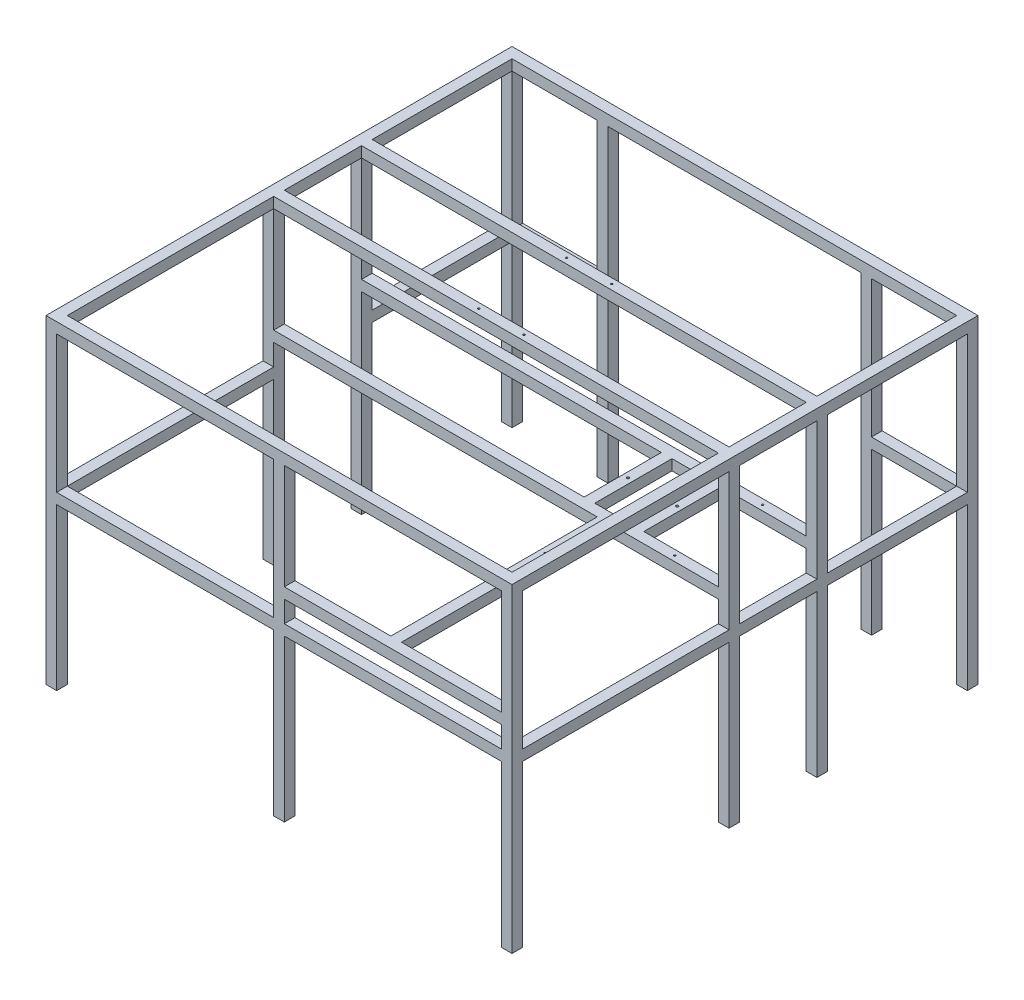
SolidWorks part; units mm, degrees
ref_plane "Front Plane" through (0, 0, 0) normal (0, 0, 1) x (1, 0, 0)
ref_plane "Top Plane" through (0, 0, 0) normal (0, 1, 0) x (1, 0, 0)
ref_plane "Right Plane" through (0, 0, 0) normal (1, 0, 0) x (0, 0, -1)
sketch "Sketch1" plane through (0, 0, 0) normal (0, 1, 0) x (1, 0, 0)
  line L0 (-835, 835) -> (-835, 310)
  line L1 (-875, 875) -> (875, 875)
  line L2 (-875, 875) -> (-875, -875)
  line L3 (-875, -875) -> (875, -875)
  line L4 (875, 875) -> (875, -875)
  line L5 (-875, 875) -> (875, -875) construction
  line L6 (-875, -875) -> (875, 875) construction
  line L7 (-835, -835) -> (835, -835)
  line L8 (835, 835) -> (835, 310)
  line L9 (-835, 835) -> (835, 835)
  line L10 (-835, -20) -> (835, -20)
  line L12 (-835, -60) -> (-835, -835)
  line L13 (-835, 835) -> (-835, -835) construction
  line L14 (835, -60) -> (835, -835)
  line L15 (835, 835) -> (835, -835) construction
  line L16 (835, 20) -> (835, -20)
  line L17 (-835, 20) -> (-835, -20)
  line L18 (-835, -60) -> (835, -60)
  line L19 (835, 270) -> (-835, 270)
  line L20 (835, 310) -> (-835, 310)
  line L21 (835, 270) -> (835, 20)
  line L22 (-835, 270) -> (-835, 20)
  point P0 (0, 0)
  dimension "D1" = 1750
  dimension "D2" = 1750
  dimension "D4" = 40
  dimension "D5" = 20
  dimension "D6" = 40
  dimension "D7" = 40
  dimension "D8" = 290
  dimension "D9" = 40
  dimension "D3" = 40
extrude "Boss-Extrude1" add sketch "Sketch1" along normal blind 40
sketch "Sketch2" plane through (0, 0, 0) normal (0, -1, 0) x (1, 0, 0)
  line L0 (0, 0) -> (0, 835) construction
  line L1 (-835, 835) -> (-875, 835)
  line L2 (-835, 835) -> (-835, 875)
  line L3 (-835, 875) -> (-875, 875)
  line L4 (-875, 835) -> (-875, 875)
  line L5 (835, 835) -> (875, 835)
  line L6 (835, 835) -> (835, 875)
  line L7 (835, 875) -> (875, 875)
  line L8 (875, 835) -> (875, 875)
  line L9 (-835, 835) -> (835, 835) construction
  line L10 (-875, 875) -> (875, 875) construction
  line L11 (20, 835) -> (-20, 835)
  line L12 (20, 835) -> (20, 875)
  line L13 (20, 875) -> (-20, 875)
  line L14 (-20, 835) -> (-20, 875)
  line L15 (875, 875) -> (875, -875) construction
  line L16 (835, 60) -> (875, 60)
  line L17 (835, 60) -> (835, 20)
  line L18 (835, 20) -> (875, 20)
  line L19 (875, 60) -> (875, 20)
  line L21 (-875, -875) -> (-875, 875) construction
  line L22 (-835, 20) -> (-875, 20)
  line L23 (-835, 20) -> (-835, 60)
  line L24 (-835, 60) -> (-875, 60)
  line L25 (-875, 20) -> (-875, 60)
  line L26 (835, 20) -> (835, -270) construction
  line L27 (835, -835) -> (-835, -835) construction
  line L28 (-875, -875) -> (-835, -875)
  line L29 (-875, -875) -> (-875, -835)
  line L30 (-875, -835) -> (-835, -835)
  line L31 (-835, -875) -> (-835, -835)
  line L32 (835, -835) -> (875, -835)
  line L33 (835, -835) -> (835, -875)
  line L34 (835, -875) -> (875, -875)
  line L35 (875, -835) -> (875, -875)
  line L36 (475, -835) -> (515, -835)
  line L37 (475, -835) -> (475, -875)
  line L38 (475, -875) -> (515, -875)
  line L39 (515, -835) -> (515, -875)
  line L40 (875, -875) -> (-875, -875) construction
  line L41 (-835, -835) -> (-835, -310) construction
  line L42 (-515, -835) -> (-475, -835)
  line L43 (-515, -835) -> (-515, -875)
  line L44 (-515, -875) -> (-475, -875)
  line L45 (-475, -835) -> (-475, -875)
  line L46 (-875, -310) -> (-835, -310)
  line L47 (-875, -310) -> (-875, -270)
  line L48 (-875, -270) -> (-835, -270)
  line L49 (-835, -310) -> (-835, -270)
  line L50 (-855, -105) -> (-855, 20) construction
  line L51 (-855, -105) -> (875, -105) construction
  line L52 (875, -270) -> (835, -270)
  line L53 (875, -270) -> (875, -310)
  line L54 (875, -310) -> (835, -310)
  line L55 (835, -270) -> (835, -310)
  dimension "D1" = 40
  dimension "D2" = 20
  dimension "D3" = 40
  dimension "D4" = 320
  dimension "D5" = 40
  dimension "D6" = 320
  dimension "D7" = 40
  dimension "D8" = 40
  dimension "D9" = 40
  dimension "D10" = 165
  dimension "D11" = 730
  dimension "D12" = 40
  dimension "D13" = 40
  dimension "D14" = 40
  dimension "D15" = 125
extrude "Boss-Extrude2" add sketch "Sketch2" along normal blind 1160
sketch "Sketch3" plane through (0, 0, 875) normal (0, 0, 1) x (1, 0, 0)
  line L0 (-875, 40) -> (-875, -1160) construction
  line L1 (-875, -515) -> (-835, -515)
  line L2 (-875, -515) -> (-875, -555)
  line L3 (-875, -555) -> (-835, -555)
  line L4 (-835, -515) -> (-835, -555)
  line L5 (-835, -1160) -> (-835, 0) construction
  line L12 (835, -1160) -> (835, 0) construction
  line L13 (835, -515) -> (875, -515)
  line L14 (835, -515) -> (835, -555)
  line L15 (835, -555) -> (875, -555)
  line L16 (875, -515) -> (875, -555)
  line L17 (875, 40) -> (875, -1160) construction
  line L18 (-835, -1160) -> (-875, -1160) construction
  dimension "D1" = 40
  dimension "D3" = 40
  dimension "D4" = 605
extrude "Boss-Extrude3" add sketch "Sketch3" against normal up to surface (1710 mm away) up to face at (-855, -580, -835)
sketch "Sketch4" plane through (-875, 0, 0) normal (-1, 0, 0) x (0, 0, 1)
  line L0 (875, 40) -> (875, -1160) construction
  line L1 (835, -555) -> (875, -555)
  line L2 (835, -555) -> (835, -515)
  line L3 (835, -515) -> (875, -515)
  line L4 (875, -555) -> (875, -515)
  line L5 (60, -515) -> (835, -515) construction
extrude "Boss-Extrude4" add sketch "Sketch4" against normal up to surface (1710 mm away) up to face at (835, -560.7143, -71.4286)
sketch "Sketch5" plane through (-875, 0, 0) normal (-1, 0, 0) x (0, 0, 1)
  line L0 (-875, 40) -> (-875, -1160) construction
  line L1 (-835, -555) -> (-875, -555)
  line L2 (-835, -555) -> (-835, -515)
  line L3 (-835, -515) -> (-875, -515)
  line L4 (-875, -555) -> (-875, -515)
  line L5 (-835, -515) -> (-310, -515) construction
extrude "Boss-Extrude5" add sketch "Sketch5" against normal up to surface (1710 mm away) up to face at (835, -857.5, 855)
sketch "Sketch6" plane through (0, 0, -875) normal (0, 0, -1) x (-1, 0, 0)
  line L1 (-475, -515) -> (475, -515)
  line L2 (-475, -515) -> (-475, -555)
  line L3 (-475, -555) -> (475, -555)
  line L4 (475, -515) -> (475, -555)
extrude "Cut-Extrude1" cut sketch "Sketch6" against normal blind 40
sketch "Sketch9" plane through (-875, 0, 0) normal (-1, 0, 0) x (0, 0, 1)
  line L1 (-270, -515) -> (20, -515)
  line L2 (-270, -515) -> (-270, -555)
  line L3 (-270, -555) -> (20, -555)
  line L4 (20, -515) -> (20, -555)
extrude "Cut-Extrude4" cut sketch "Sketch9" against normal blind 40
sketch "Sketch10" plane through (0, 40, 0) normal (0, 1, 0) x (1, 0, 0)
  line L0 (835, -60) -> (-835, -60) construction
  line L1 (-835, 310) -> (835, 310) construction
  circle A0 centre (85, -40) radius 4
  circle A1 centre (-85, -40) radius 4
  circle A2 centre (-85, 290) radius 4
  circle A3 centre (85, 290) radius 4
  dimension "D1" = 170
  dimension "D2" = 85
  dimension "D3" = 8
  dimension "D4" = 8
  dimension "D5" = 8
  dimension "D6" = 8
  dimension "D7" = 20
  dimension "D8" = 20
hole_wizard "M8 Tapped Hole1" positions "Sketch11" profile "Sketch12" tap size "M8" standard "ISO"
sketch "Sketch11" plane through (0, 40, 0) normal (0, 1, 0) x (1, 0, 0)
  point P0 (85, -40)
  point P3 (-85, -40)
  point P6 (-85, 290)
  point P9 (85, 290)
sketch "Sketch12" plane through (85, 40, 40) normal (1, 0, 0) x (0, 0, 1)
  line L0 (0, 0) -> (0, 19.75)
  line L1 (0, 19.75) -> (3.4, 17.7071)
  line L2 (3.4, 17.7071) -> (3.4, 0)
  line L5 (3.4, 0) -> (0, 0)
  line L10 (0, 19.75) -> (-3.4, 17.7071) construction
  line L11 (0, -6.35) -> (0, 107.95) construction
  dimension "Tap Drill Dia." = 6.8
  dimension "Tap Drill Depth" = 19.75
  dimension "Drill Angle" = 118
cosmetic thread "Hole Thread1" parameters "D1"=16, "D2"=8
cosmetic thread "Hole Thread2" parameters "D1"=16, "D2"=8
cosmetic thread "Hole Thread3" parameters "D1"=16, "D2"=8
cosmetic thread "Hole Thread4" parameters "D1"=16, "D2"=8
sketch "Sketch13" plane through (875, 0, 0) normal (1, 0, 0) x (0, 0, -1)
  line L0 (-60, -515) -> (-60, 0) construction
  line L1 (-60, -395) -> (-20, -395)
  line L2 (-60, -395) -> (-60, -435)
  line L3 (-60, -435) -> (-20, -435)
  line L4 (-20, -395) -> (-20, -435)
  line L5 (-20, -515) -> (-20, 0) construction
  line L6 (270, -515) -> (270, 0) construction
  line L7 (270, -395) -> (310, -395)
  line L8 (270, -395) -> (270, -435)
  line L9 (270, -435) -> (310, -435)
  line L10 (310, -395) -> (310, -435)
  line L11 (310, -515) -> (310, 0) construction
  line L12 (270, -515) -> (-20, -515) construction
  line L13 (-875, 40) -> (-875, -1160) construction
  line L14 (-875, -395) -> (-835, -395)
  line L15 (-875, -395) -> (-875, -435)
  line L16 (-875, -435) -> (-835, -435)
  line L17 (-835, -395) -> (-835, -435)
  line L18 (-835, -515) -> (-835, 0) construction
  dimension "D1" = 40
  dimension "D2" = 80
  dimension "D3" = 40
extrude "Boss-Extrude6" add sketch "Sketch13" against normal up to surface (1710 mm away) up to face at (-835, -557.5, -431.25)
sketch "Sketch15" plane through (0, 0, 875) normal (0, 0, 1) x (1, 0, 0)
  line L1 (-835, -395) -> (-20, -395)
  line L2 (-835, -395) -> (-835, -435)
  line L3 (-835, -435) -> (-20, -435)
  line L4 (-20, -395) -> (-20, -435)
extrude "Cut-Extrude5" cut sketch "Sketch15" against normal blind 40
sketch "Sketch16" plane through (0, 0, 875) normal (0, 0, 1) x (1, 0, 0)
  line L0 (20, -395) -> (835, -395) construction
  line L1 (380, -395) -> (420, -395)
  line L2 (380, -395) -> (380, -435)
  line L3 (380, -435) -> (420, -435)
  line L4 (420, -395) -> (420, -435)
  line L5 (20, -435) -> (835, -435) construction
  line L6 (20, -515) -> (20, -435) construction
  dimension "D1" = 40
  dimension "D2" = 400
extrude "Boss-Extrude7" add sketch "Sketch16" against normal up to surface (815 mm away) up to face at (855, -857.5, 60)
ref_plane "Plane1" through (380, -395, 835) normal (0, 0, 1) x (1, 0, 0)
sketch "Sketch18" plane through (0, -395, 0) normal (0, 1, 0) x (1, 0, 0)
  line L0 (0, 125) -> (504.8879, -379.8879) construction
  line L1 (420, -60) -> (420, -835) construction
  line L2 (0, 125) -> (0, 0) construction
  circle A0 centre (400, -275) radius 3.3
  dimension "D1" = 6.6
  dimension "D2" = 20
  dimension "D3" = 45
extrude "Cut-Extrude6" cut sketch "Sketch18" against normal blind 40
sketch "Sketch20" plane through (0, -395, 0) normal (0, 1, 0) x (1, 0, 0)
  line L0 (675, -9.2658) -> (607.6127, -171.9532) construction
  line L1 (675, -9.2658) -> (572.2374, -257.3568) construction
  line L2 (-835, -20) -> (835, -20) construction
  line L3 (835, 270) -> (-835, 270) construction
  circle A0 centre (651.4456, -40) radius 3.3
  circle A1 centre (651.4456, 290) radius 3.3
  dimension "D1" = 6.6
  dimension "D2" = 10
  dimension "D3" = 20
  dimension "D4" = 6.6
  dimension "D5" = 20
extrude "Cut-Extrude8" cut sketch "Sketch20" against normal blind 40
sketch "Sketch22" plane through (0, 0, 60) normal (0, 0, 1) x (1, 0, 0)
  line L0 (420, -395) -> (420, -435) construction
  line L1 (400, -435) -> (428.2843, -435) construction
  line L2 (420, -435) -> (385.8579, -435) construction
  line L3 (371.7157, -435) -> (400, -435) construction
  line L4 (385.8579, -435) -> (385.8579, -395) construction
  line L5 (20, -395) -> (835, -395) construction
  line L6 (385.8579, -395) -> (420, -395) construction
  line L7 (402.9289, -395) -> (402.9289, -435) construction
  line L8 (475, -395) -> (475, -435)
  line L9 (330.8579, -395) -> (330.8579, -435)
  line L10 (20, -435) -> (835, -435) construction
  line L11 (475, -435) -> (515, -435)
  line L12 (515, -435) -> (515, -395)
  line L13 (515, -395) -> (475, -395)
  line L14 (330.8579, -435) -> (290.8579, -435)
  line L15 (290.8579, -435) -> (290.8579, -395)
  line L16 (290.8579, -395) -> (330.8579, -395)
  dimension "D1" = 55
  dimension "D2" = 55
  dimension "D3" = 40
  dimension "D4" = 40
extrude "Boss-Extrude8" add sketch "Sketch22" against normal up to surface (330 mm away) up to face at (0, -417.5, -270)
sketch "Sketch23" plane through (0, -395, 0) normal (0, 1, 0) x (1, 0, 0)
  line L0 (835, 270) -> (-835, 270) construction
  line L1 (330.8579, 270) -> (330.8579, -20) construction
  line L2 (475, 270) -> (475, -20) construction
  circle A0 centre (310.8579, 125) radius 4.5
  circle A1 centre (495, 125) radius 4.5
  point P8 (0, 0)
  dimension "D1" = 145
  dimension "D2" = 20
  dimension "D3" = 9
  dimension "D4" = 9
  dimension "D5" = 20
extrude "Cut-Extrude9" cut sketch "Sketch23" against normal blind 40
